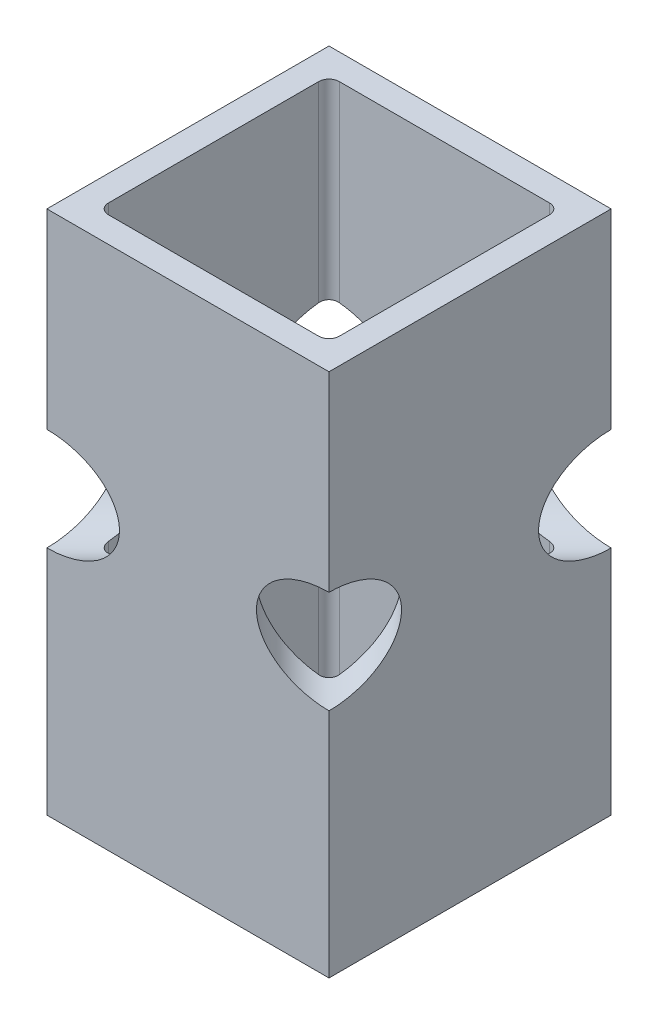
SolidWorks part; units mm, degrees
ref_plane "Front Plane" through (0, 0, 0) normal (0, 0, 1) x (1, 0, 0)
ref_plane "Top Plane" through (0, 0, 0) normal (0, 1, 0) x (1, 0, 0)
ref_plane "Right Plane" through (0, 0, 0) normal (1, 0, 0) x (0, 0, -1)
sketch "Sketch1" plane through (0, 0, 0) normal (0, 1, 0) x (1, 0, 0)
  line L0 (17.4625, 17.4625) -> (-17.4625, 17.4625)
  line L1 (14.2875, 14.2875) -> (-14.2875, 14.2875)
  line L2 (14.2875, 14.2875) -> (14.2875, -14.2875)
  line L3 (14.2875, -14.2875) -> (-14.2875, -14.2875)
  line L4 (-14.2875, 14.2875) -> (-14.2875, -14.2875)
  line L5 (14.2875, 14.2875) -> (-14.2875, -14.2875) construction
  line L6 (14.2875, -14.2875) -> (-14.2875, 14.2875) construction
  line L7 (-17.4625, 17.4625) -> (-17.4625, -17.4625)
  line L8 (17.4625, -17.4625) -> (-17.4625, -17.4625)
  line L9 (17.4625, 17.4625) -> (17.4625, -17.4625)
  point P0 (0, 0)
  dimension "D1" = 28.575
  dimension "D2" = 3.175
extrude "Boss-Extrude1" add sketch "Sketch1" along normal blind 65 contours L9 L0 L7 L8 L4 L1 L2 L3
fillet "Fillet1" radius 1.27 4 edges at (14.2875, 32.5, 14.2875) (-14.2875, 32.5, 14.2875) (-14.2875, 32.5, -14.2875) (14.2875, 32.5, -14.2875)
ref_plane "Plane1" through (0, 0, 0) normal (0.7071, 0, 0.7071) x (0.7071, 0, -0.7071)
ref_plane "Plane2" through (0, 0, 0) normal (-0.7071, 0, 0.7071) x (0.7071, 0, 0.7071)
sketch "Sketch2" plane through (0, 0, 0) normal (-0.7071, 0, 0.7071) x (0.7071, 0, 0.7071)
  line L0 (0, 65) -> (0, 0) construction
  line L2 (24.6957, 65) -> (0, 65) construction
  circle A0 centre (0, 35) radius 6.35
  dimension "D1" = 12.7
  dimension "D2" = 30
extrude "Cut-Extrude1" cut sketch "Sketch2" against normal through all and the other way through all
sketch "Sketch3" plane through (0, 0, 0) normal (0.7071, 0, 0.7071) x (0.7071, 0, -0.7071)
  line L0 (0, 19.0565) -> (0, -19.0565) construction
  circle A0 centre (0, 35) radius 6.35
  arc A1 (-24.6957, 28.65) -> (-24.6957, 41.35) centre (-24.6957, 35) ccw construction
  arc A2 (-24.6957, 28.65) -> (-24.6957, 41.35) centre (-24.6957, 35) ccw
extrude "Cut-Extrude2" cut sketch "Sketch3" against normal through all and the other way through all contours A0
